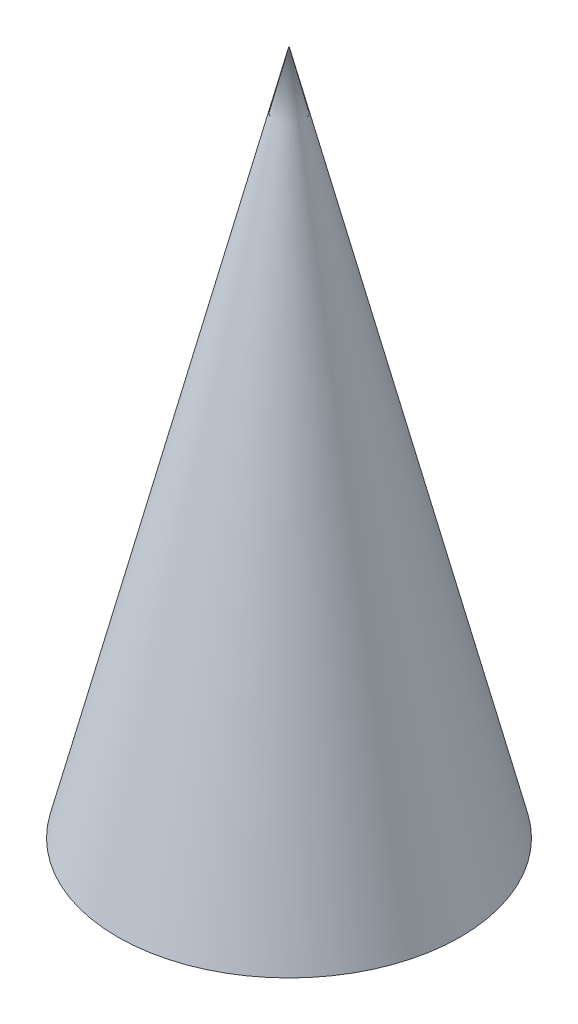
SolidWorks part; units mm, degrees
ref_plane "Front" through (0, 0, 0) normal (0, 0, 1) x (1, 0, 0)
ref_plane "Top" through (0, 0, 0) normal (0, 1, 0) x (1, 0, 0)
ref_plane "Right" through (0, 0, 0) normal (1, 0, 0) x (0, 0, -1)
sketch "Sketch1" plane through (0, 0, 0) normal (0, 1, 0) x (1, 0, 0)
  circle A0 centre (0, 0) radius 5
  dimension "D1" = 10
sketch "Sketch2" plane through (0, 0, 0) normal (0, 0, 1) x (1, 0, 0)
  point P0 (0, 20)
  dimension "D1" = 20
loft "Loft1" add profiles "Sketch2", "Sketch1"
